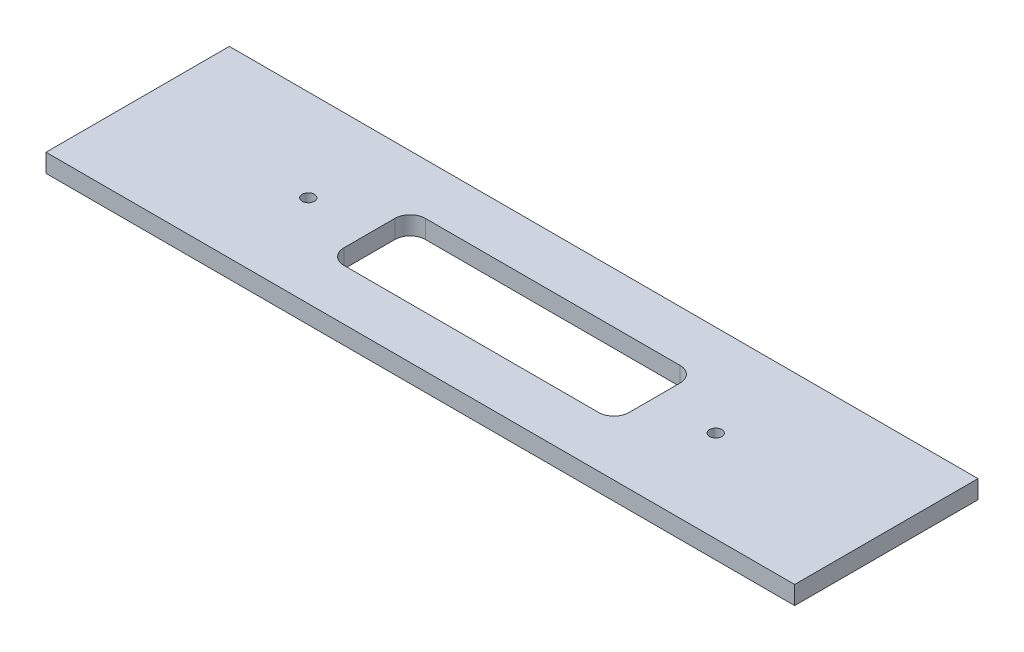
SolidWorks part; units mm, degrees
ref_plane "Front Plane" through (0, 0, 0) normal (0, 0, 1) x (1, 0, 0)
ref_plane "Top Plane" through (0, 0, 0) normal (0, 1, 0) x (1, 0, 0)
ref_plane "Right Plane" through (0, 0, 0) normal (1, 0, 0) x (0, 0, -1)
sketch "Sketch1" plane through (0, 0, 0) normal (0, 1, 0) x (1, 0, 0)
  line L1 (-367.5, -90) -> (367.5, -90)
  line L2 (-367.5, -90) -> (-367.5, 90)
  line L3 (-367.5, 90) -> (367.5, 90)
  line L4 (367.5, -90) -> (367.5, 90)
  line L5 (-367.5, -90) -> (367.5, 90) construction
  line L6 (-367.5, 90) -> (367.5, -90) construction
  point P0 (0, 0)
  dimension "D1" = 735
  dimension "D2" = 180
extrude "Boss-Extrude1" add sketch "Sketch1" along normal blind 18
sketch "Sketch2" plane through (0, 18, 0) normal (0, 1, 0) x (1, 0, 0)
  line L1 (-125, -40) -> (125, -40)
  line L2 (-140, -25) -> (-140, 25)
  line L3 (-125, 40) -> (125, 40)
  line L4 (140, -25) -> (140, 25)
  line L5 (-140, -40) -> (140, 40) construction
  line L6 (-140, 40) -> (140, -40) construction
  arc A0 (-125, -40) -> (-140, -25) centre (-125, -25) cw
  arc A1 (125, -40) -> (140, -25) centre (125, -25) ccw
  arc A2 (125, 40) -> (140, 25) centre (125, 25) cw
  arc A3 (-140, 25) -> (-125, 40) centre (-125, 25) cw
  circle A4 centre (-200, 0) radius 6
  circle A5 centre (200, 0) radius 6
  point P0 (0, 0)
  dimension "D3" = 15
  dimension "D4" = 12
  dimension "D5" = 12
  dimension "D6" = 200
  dimension "D7" = 200
  dimension "D1" = 80
  dimension "D2" = 280
extrude "Cut-Extrude1" cut sketch "Sketch2" against normal blind 60
